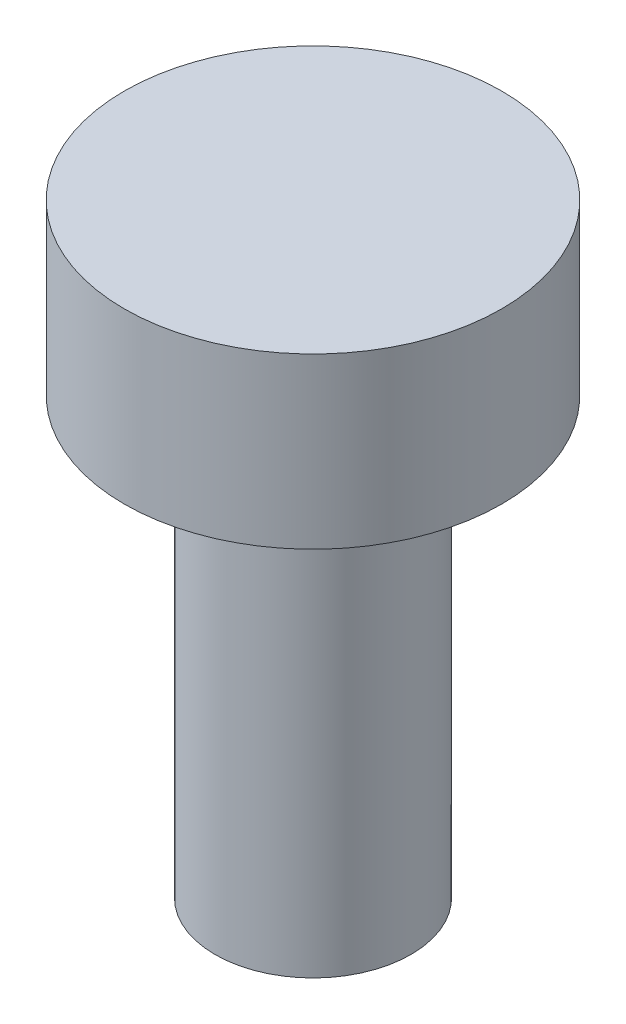
SolidWorks part; units mm, degrees
ref_plane "Front Plane" through (0, 0, 0) normal (0, 0, 1) x (1, 0, 0)
ref_plane "Top Plane" through (0, 0, 0) normal (0, 1, 0) x (1, 0, 0)
ref_plane "Right Plane" through (0, 0, 0) normal (1, 0, 0) x (0, 0, -1)
sketch "Sketch1" plane through (0, 0, 0) normal (0, 1, 0) x (1, 0, 0)
  circle A0 centre (0, 0) radius 1.35
  dimension "D1" = 2.7
extrude "Boss-Extrude1" add sketch "Sketch1" along normal blind 6
sketch "Sketch2" plane through (0, 6, 0) normal (0, 1, 0) x (1, 0, 0)
  circle A0 centre (0, 0) radius 2.6
  dimension "D1" = 5.2
extrude "Boss-Extrude2" add sketch "Sketch2" along normal blind 2.33
